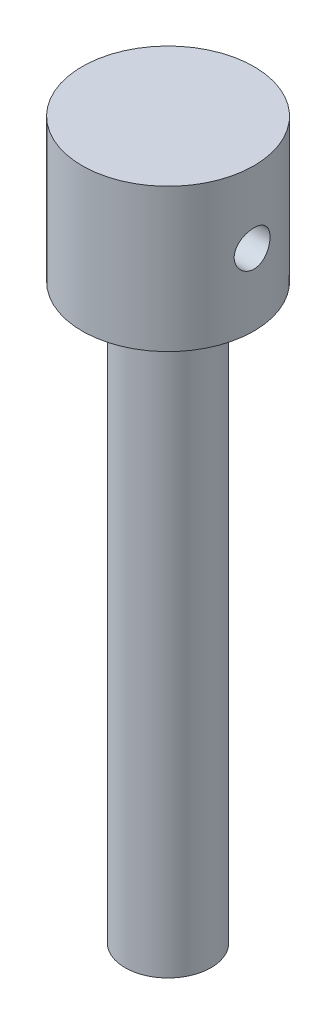
SolidWorks part; units mm, degrees
material "1060 Alloy"
ref_plane "Front Plane" through (0, 0, 0) normal (0, 0, 1) x (1, 0, 0)
ref_plane "Top Plane" through (0, 0, 0) normal (0, 1, 0) x (1, 0, 0)
ref_plane "Right Plane" through (0, 0, 0) normal (1, 0, 0) x (0, 0, -1)
sketch "Sketch1" plane through (0, 0, 0) normal (0, 0, 1) x (1, 0, 0)
  line L0 (0, -1000) -> (0, 49000) construction
  line L1 (0, 0) -> (6, 0)
  line L2 (6, 0) -> (6, 80)
  line L3 (6, 80) -> (12, 80)
  line L4 (12, 80) -> (12, 100)
  line L5 (12, 100) -> (0, 100)
  line L6 (0, 0) -> (0, 100)
  dimension "D1" = 6
  dimension "D2" = 80
  dimension "D3" = 12
  dimension "D4" = 20
revolve "Revolve1" add sketch "Sketch1" angle 360 about L0
ref_plane "Plane1" through (12, 0, 0) normal (1, 0, 0) x (0, 0, -1)
sketch "Sketch2" plane through (12, 0, 0) normal (1, 0, 0) x (0, 0, -1)
  line L0 (0, -900) -> (0, 49100) construction
  line L1 (12, 100) -> (-12, 100) construction
  line L2 (-988, 90) -> (49012, 90) construction
  line L3 (12, 80) -> (12, 100) construction
  circle A0 centre (0, 90) radius 2.5
  point P5 (0, 100)
  point P10 (12, 90)
  dimension "D1" = 5
extrude "Cut-Extrude1" cut sketch "Sketch2" against normal through all
